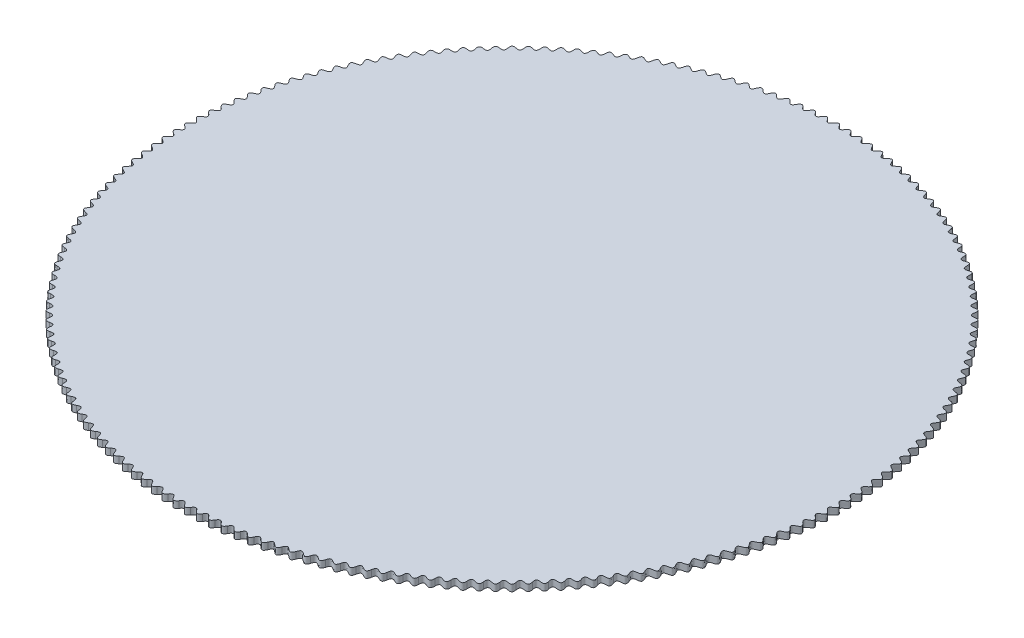
SolidWorks part; units mm, degrees
ref_plane "Ebene vorne" through (0, 0, 0) normal (0, 0, 1) x (1, 0, 0)
ref_plane "Ebene oben" through (0, 0, 0) normal (0, 1, 0) x (1, 0, 0)
ref_plane "Ebene rechts" through (0, 0, 0) normal (1, 0, 0) x (0, 0, -1)
sketch "Skizze1" plane through (0, 0, 0) normal (0, 1, 0) x (1, 0, 0)
  circle A0 centre (0, 0) radius 50
  dimension "D1" = 100
extrude "Aufsatz-Linear austragen1" add sketch "Skizze1" along normal blind 1
sketch "Skizze2" plane through (0, 1, 0) normal (0, 1, 0) x (1, 0, 0)
  line L0 (0, 0) -> (-0.8826, 50) construction
  line L1 (-0.8737, 49.5) -> (0.8737, 49.5) construction
  line L2 (0.8826, 50) -> (0, 0) construction
  line L3 (0, 0) -> (0, -51.9832) construction
  line L4 (-0.8737, 49.5) -> (0, 50.75) construction
  line L5 (0, 50.75) -> (0, 48.25) construction
  line L6 (0, 48.25) -> (0.8737, 49.5) construction
  line L7 (-0.8737, 49.5) -> (-0.8826, 50)
  line L8 (-0.8826, 50) -> (0.8826, 50)
  line L9 (0.8826, 50) -> (0.8737, 49.5)
  circle A1 centre (0, 0) radius 50 construction
  spline S0 degree 3 poles (-0.8737, 49.5) (0, 50.75) (0, 48.25) (0.8737, 49.5) knots 0 0 0 0 1 1 1 1
  point P9 (0, 49.5)
  dimension "D1" = 2.022
  dimension "D2" = 0.5
  dimension "D3" = 2.5
extrude "Schnitt-Linear austragen1" cut sketch "Skizze2" against normal through all
pattern_circular "Kreismuster1" count 178 over 360 about axis through (0, 1, 0) along (0, 1, 0) of "Schnitt-Linear austragen1"
